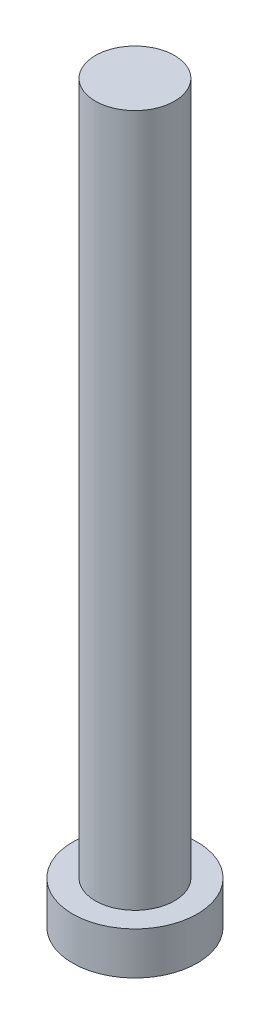
SolidWorks part; units mm, degrees
ref_plane "前视基准面" through (0, 0, 0) normal (0, 0, 1) x (1, 0, 0)
ref_plane "上视基准面" through (0, 0, 0) normal (0, 1, 0) x (1, 0, 0)
ref_plane "右视基准面" through (0, 0, 0) normal (1, 0, 0) x (0, 0, -1)
sketch "草图1" plane through (0, 0, 0) normal (0, 1, 0) x (1, 0, 0)
  circle A0 centre (0, 0) radius 3.15
extrude "凸台-拉伸1" add sketch "草图1" along normal blind 2.15
sketch "草图2" plane through (0, 2.15, 0) normal (0, 1, 0) x (1, 0, 0)
  circle A0 centre (0, 0) radius 2
extrude "凸台-拉伸2" add sketch "草图2" along normal blind 35
sketch "草图3" plane through (0, 0, 0) normal (0, -1, 0) x (1, 0, 0)
  line L0 (-0.5, 1) -> (-0.5, 2)
  line L1 (-2, -0.5) -> (-1, -0.5)
  line L2 (-2, -0.5) -> (-2, 0.5)
  line L3 (-2, 0.5) -> (-1, 0.5)
  line L4 (2, -0.5) -> (2, 0.5)
  line L5 (-2, -0.5) -> (2, 0.5) construction
  line L6 (-2, 0.5) -> (2, -0.5) construction
  line L7 (-0.5, -2) -> (0.5, -2)
  line L8 (-0.5, -2) -> (-0.5, -1)
  line L9 (-0.5, 2) -> (0.5, 2)
  line L10 (0.5, -2) -> (0.5, -1)
  line L11 (-0.5, -2) -> (0.5, 2) construction
  line L12 (-0.5, 2) -> (0.5, -2) construction
  line L13 (1, -0.5) -> (2, -0.5)
  line L14 (0.5, 1) -> (0.5, 2)
  line L15 (1, 0.5) -> (2, 0.5)
  arc A0 (-0.5, -1) -> (-1, -0.5) centre (-1, -1) ccw
  arc A1 (1, -0.5) -> (0.5, -1) centre (1, -1) ccw
  arc A2 (0.5, 1) -> (1, 0.5) centre (1, 1) ccw
  arc A3 (-0.5, 1) -> (-1, 0.5) centre (-1, 1) cw
  point P0 (0, 0)
  point P6 (0, 0)
  point P21 (0.5, 0.5)
  dimension "D1" = 0.5
extrude "切除-拉伸1" cut sketch "草图3" against normal blind 1.5
